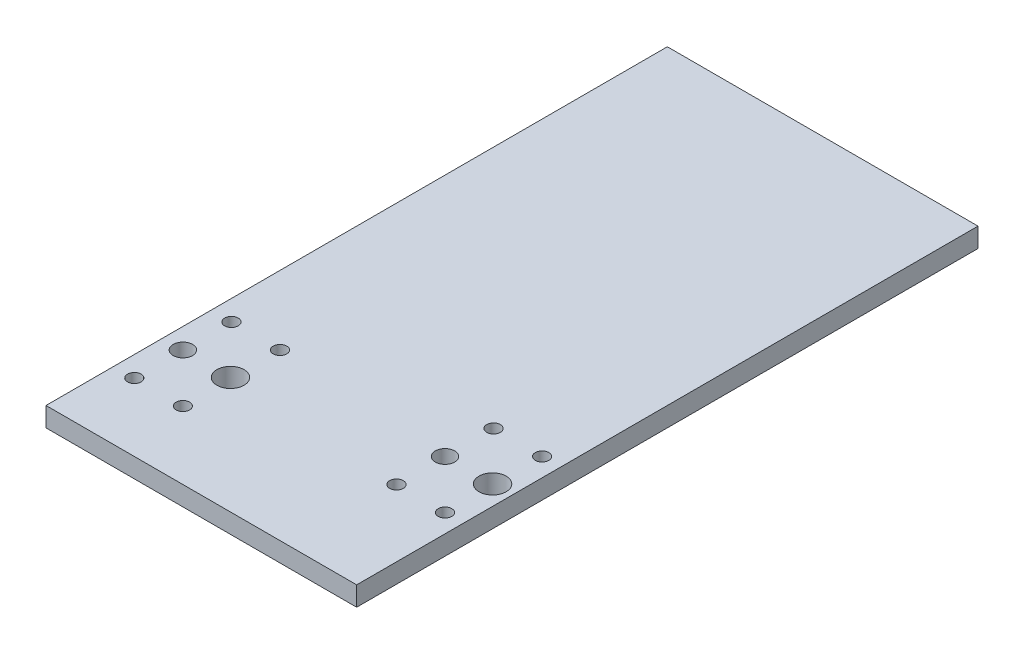
SolidWorks part; units mm, degrees
material "PBT Общее назначение"
ref_plane "Спереди" through (0, 0, 0) normal (0, 0, 1) x (1, 0, 0)
ref_plane "Сверху" through (0, 0, 0) normal (0, 1, 0) x (1, 0, 0)
ref_plane "Справа" through (0, 0, 0) normal (1, 0, 0) x (0, 0, -1)
sketch "Эскиз1" plane through (0, 0, 0) normal (0, 1, 0) x (1, 0, 0)
  line L0 (0, 2.6093) -> (16, 2.6093)
  line L3 (0, 34.6093) -> (16, 34.6093)
  line L4 (16, 2.6093) -> (16, 34.6093)
  line L5 (0, 2.6093) -> (0, 34.6093)
  dimension "D1" = 32
  dimension "D2" = 16
extrude "Бобышка-Вытянуть1" add sketch "Эскиз1" along normal blind 1
sketch "Эскиз2" plane through (0, 1, 0) normal (0, 1, 0) x (1, 0, 0)
  line L2 (16, 34.6093) -> (0, 34.6093) construction
  line L3 (16, 2.6093) -> (16, 34.6093) construction
  circle A0 centre (15, 10.6093) radius 0.7
  circle A1 centre (12.55, 10.6093) radius 0.5
  circle A2 centre (3.5, 8.6093) radius 0.7
  circle A3 centre (1.05, 8.6093) radius 0.5
  circle A4 centre (12.55, 13.1093) radius 0.35
  circle A5 centre (15.05, 13.1093) radius 0.35
  circle A6 centre (15.05, 8.1093) radius 0.35
  circle A7 centre (12.55, 8.1093) radius 0.35
  circle A8 centre (3.55, 11.1093) radius 0.35
  circle A9 centre (1.05, 11.1093) radius 0.35
  circle A10 centre (1.05, 6.1093) radius 0.35
  circle A11 centre (3.55, 6.1093) radius 0.35
  dimension "D1" = 2.45
  dimension "D2" = 2.45
  dimension "D3" = 11.5
  dimension "D4" = 2
  dimension "D5" = 1.4
  dimension "D6" = 1
  dimension "D7" = 1
  dimension "D8" = 26
  dimension "D9" = 2.5
  dimension "D10" = 2.5
  dimension "D11" = 0.7
  dimension "D12" = 2.5
  dimension "D13" = 2.5
  dimension "D14" = 5
  dimension "D15" = 5
extrude "Вырез-Вытянуть1" cut sketch "Эскиз2" against normal through all
